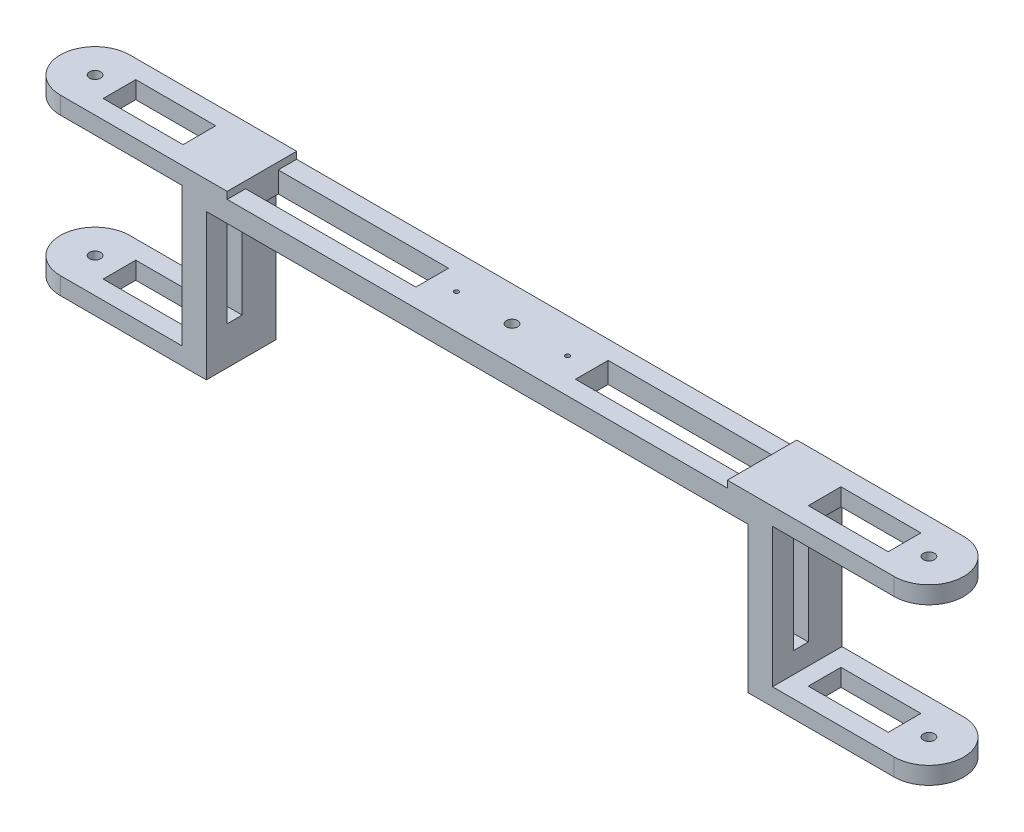
SolidWorks part; units mm, degrees
ref_plane "前视基准面" through (0, 0, 0) normal (0, 0, 1) x (1, 0, 0)
ref_plane "上视基准面" through (0, 0, 0) normal (0, 1, 0) x (1, 0, 0)
ref_plane "右视基准面" through (0, 0, 0) normal (1, 0, 0) x (0, 0, -1)
sketch "草图1" plane through (0, 0, 0) normal (0, 1, 0) x (1, 0, 0)
  line L0 (-79.187, 0) -> (77.2358, 0) construction
  line L1 (-163.252, 10) -> (76.748, 10)
  line L2 (-163.252, -10) -> (76.748, -10)
  line L3 (-43.252, 10) -> (-43.252, -10) construction
  circle A1 centre (76.748, 0) radius 1.6
  circle A2 centre (-163.252, 0) radius 1.6
  circle A4 centre (-59.252, 0) radius 0.64
  circle A5 centre (-43.252, 0) radius 1.6
  circle A6 centre (-27.252, 0) radius 0.64
  arc A7 (-163.252, 10) -> (-163.252, -10) centre (-163.252, 0) ccw
  arc A8 (76.748, -10) -> (76.748, 10) centre (76.748, 0) ccw
  dimension "D3" = 16
  dimension "D4" = 240
  dimension "D1" = 10
extrude "凸台-拉伸1" add sketch "草图1" along normal blind 50
sketch "草图4" plane through (0, 0, -10) normal (0, 0, -1) x (-1, 0, 0)
  line L0 (-86.7225, 45) -> (-56.748, 45)
  line L2 (-56.748, 5) -> (-86.748, 5)
  line L3 (-86.748, 50) -> (-86.748, 0) construction
  line L4 (-76.748, 50) -> (-86.748, 50) construction
  line L5 (-76.748, 0) -> (163.252, 0) construction
  line L6 (-86.748, 25) -> (173.252, 25) construction
  line L7 (173.252, 0) -> (173.252, 50) construction
  line L8 (43.252, 50) -> (43.252, 0) construction
  line L9 (-76.748, 50) -> (163.252, 50) construction
  line L10 (128.2266, 5) -> (173.252, 5)
  line L12 (173.2266, 45) -> (128.2266, 45)
  line L16 (-34.7225, 42) -> (121.2266, 42)
  line L17 (173.252, 5) -> (178.6264, 5)
  line L18 (-34.7225, 0) -> (121.2266, 0)
  line L20 (178.6264, 5) -> (178.6264, 45)
  line L21 (178.6264, 45) -> (173.2266, 45)
  line L22 (-86.748, 5) -> (-94.6899, 5)
  line L23 (-94.6899, 5) -> (-94.6899, 45)
  line L24 (-94.6899, 45) -> (-86.7225, 45)
  line L25 (-59.3737, 45) -> (193.1251, 45) construction
  line L26 (-86.748, 5) -> (206.5693, 5) construction
  line L27 (-34.7225, 42) -> (-34.7225, 0)
  line L28 (-41.7225, 45) -> (-41.7225, 5)
  line L29 (-56.748, 45) -> (-41.7225, 45)
  line L30 (-56.748, 5) -> (-41.7225, 5)
  line L31 (128.2266, 45) -> (128.2266, 5)
  line L32 (121.2266, 42) -> (121.2266, 0)
  dimension "D1" = 5
  dimension "D2" = 5
  dimension "D3" = 45
  dimension "D4" = 7
  dimension "D5" = 8
extrude "切除-拉伸3" cut sketch "草图4" against normal through all
sketch "草图5" plane through (0, 0, 0) normal (0, -1, 0) x (1, 0, 0)
  line L0 (86.748, 0) -> (-173.252, 0) construction
  line L1 (46.7225, 4.7008) -> (69.7225, 4.7008)
  line L2 (69.7225, 4.7008) -> (69.7225, -4.7008)
  line L3 (46.7225, 4.7008) -> (46.7225, -4.7008)
  line L5 (34.7225, 10) -> (34.7225, -10) construction
  line L6 (46.7225, -4.7008) -> (69.7225, -4.7008)
  line L7 (28.7225, 4.7008) -> (28.7225, -4.7008)
  line L8 (28.7225, -4.7008) -> (-20.2775, -4.7008)
  line L9 (-20.2775, -4.7008) -> (-20.2775, 4.7008)
  line L10 (-20.2775, 4.7008) -> (28.7225, 4.7008)
  line L11 (-43.252, 10) -> (-43.252, -10) construction
  line L12 (-121.2266, 10) -> (34.7225, 10) construction
  line L13 (-121.2266, -10) -> (34.7225, -10) construction
  line L14 (-66.2266, 4.7008) -> (-115.2266, 4.7008)
  line L15 (-66.2266, -4.7008) -> (-66.2266, 4.7008)
  line L16 (-115.2266, -4.7008) -> (-66.2266, -4.7008)
  line L17 (-115.2266, 4.7008) -> (-115.2266, -4.7008)
  line L18 (-133.2266, -4.7008) -> (-156.2266, -4.7008)
  line L19 (-133.2266, 4.7008) -> (-133.2266, -4.7008)
  line L20 (-156.2266, 4.7008) -> (-156.2266, -4.7008)
  line L21 (-133.2266, 4.7008) -> (-156.2266, 4.7008)
  arc A0 (76.748, -10) -> (76.748, 10) centre (76.748, 0) ccw construction
  arc A1 (-163.252, 10) -> (-163.252, -10) centre (-163.252, 0) ccw construction
  point P15 (46.7225, 0)
  point P16 (69.7225, 0)
  point P34 (-156.2266, 0)
  point P35 (-133.2266, 0)
  dimension "D1" = 12
  dimension "D2" = 23
  dimension "D3" = 6
  dimension "D4" = 49
extrude "切除-拉伸4" cut sketch "草图5" against normal through all
sketch "草图6" plane through (-128.2266, 0, 0) normal (-1, 0, 0) x (0, 0, 1)
  line L0 (1.8377, 5) -> (1.8377, 45) construction
  line L1 (-0.3247, 11) -> (4, 11)
  line L2 (-0.3247, 11) -> (-0.3247, 39)
  line L3 (-0.3247, 39) -> (4, 39)
  line L4 (4, 11) -> (4, 39)
  line L5 (-0.3247, 11) -> (4, 39) construction
  line L6 (-0.3247, 39) -> (4, 11) construction
  line L7 (10, 45) -> (10, 5) construction
  line L8 (-10, 45) -> (10, 45) construction
  point P0 (1.8377, 25)
  dimension "D1" = 6
  dimension "D2" = 6
extrude "切除-拉伸5" cut sketch "草图6" against normal through all
sketch "草图7" plane through (0, 0, 10) normal (0, 0, 1) x (1, 0, 0)
  line L0 (-115.2266, 50) -> (-115.2266, 48)
  line L1 (-163.252, 50) -> (76.748, 50) construction
  line L2 (-115.2266, 48) -> (28.7225, 48)
  line L3 (28.7225, 48) -> (28.7225, 50)
  line L4 (28.7225, 50) -> (-115.2266, 50)
  line L5 (-121.2266, 42) -> (34.7225, 42) construction
  line L6 (41.7225, 5) -> (41.7225, 45) construction
  line L7 (-121.2266, 0) -> (-121.2266, 42) construction
  dimension "D1" = 6
  dimension "D2" = 13
  dimension "D3" = 6
extrude "切除-拉伸6" cut sketch "草图7" against normal through all
